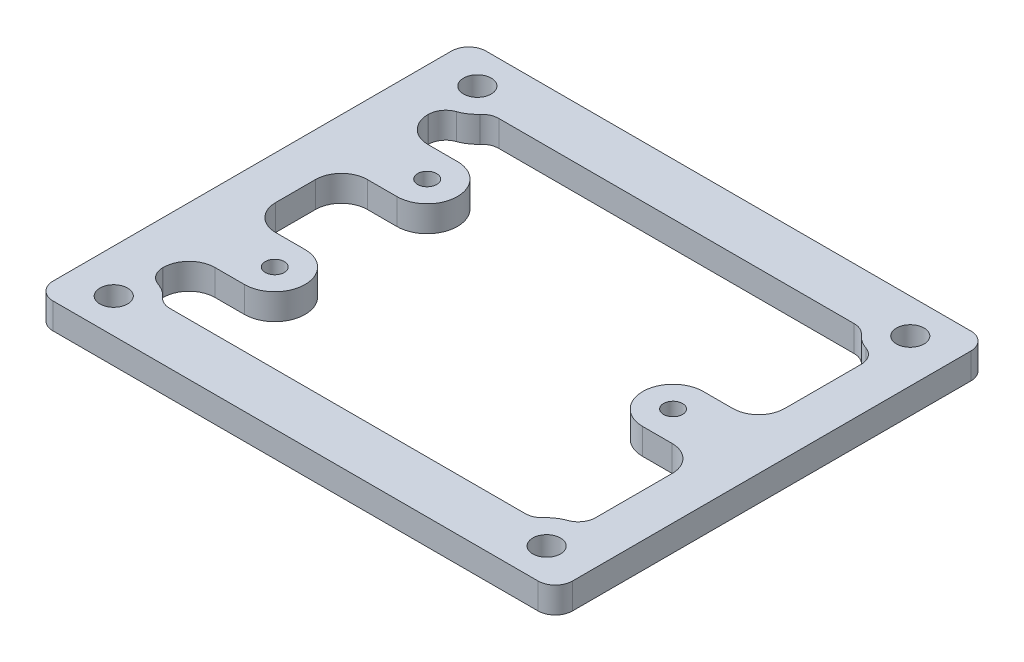
SolidWorks part; units mm, degrees
ref_plane "前视基准面" through (0, 0, 0) normal (0, 0, 1) x (1, 0, 0)
ref_plane "上视基准面" through (0, 0, 0) normal (0, 1, 0) x (1, 0, 0)
ref_plane "右视基准面" through (0, 0, 0) normal (1, 0, 0) x (0, 0, -1)
sketch "草图1" plane through (0, 0, 0) normal (0, 1, 0) x (1, 0, 0)
  line L0 (0, 0) -> (0, 11.3966) construction
  line L1 (-30, 25) -> (30, 25)
  line L2 (-30, 25) -> (-30, -25)
  line L3 (-30, -25) -> (30, -25)
  line L4 (30, 25) -> (30, -25)
  line L5 (-30, 25) -> (30, -25) construction
  line L6 (-30, -25) -> (30, 25) construction
  line L7 (0, 0) -> (7.4363, 0) construction
  line L8 (-25, -5.3) -> (-25, 5.3)
  line L9 (-25, 5.3) -> (-18.6, 5.3)
  line L10 (-25, 17) -> (-25, 12.3)
  line L11 (-25, 12.3) -> (-18.6, 12.3)
  line L12 (-21.5359, 19) -> (21.5359, 19)
  line L13 (25, 17) -> (25, 3.5)
  line L14 (25, 3.5) -> (18.6, 3.5)
  line L15 (25, -3.5) -> (18.6, -3.5)
  line L16 (25, -17) -> (25, -3.5)
  line L17 (-21.5359, -19) -> (21.5359, -19)
  line L18 (-25, -17) -> (-25, -12.3)
  line L19 (-25, -12.3) -> (-18.6, -12.3)
  line L20 (-25, -5.3) -> (-18.6, -5.3)
  circle A0 centre (-25, 21) radius 1.6
  circle A1 centre (25, 21) radius 1.6
  circle A2 centre (25, -21) radius 1.6
  circle A3 centre (-25, -21) radius 1.6
  circle A4 centre (18.6, 0) radius 1.1
  circle A5 centre (-18.6, 8.8) radius 1.1
  circle A6 centre (-18.6, -8.8) radius 1.1
  arc A7 (-18.6, 5.3) -> (-18.6, 12.3) centre (-18.6, 8.8) ccw
  arc A8 (18.6, 3.5) -> (18.6, -3.5) centre (18.6, 0) ccw
  arc A9 (-25, 17) -> (-21.5359, 19) centre (-25, 21) ccw
  arc A10 (25, 17) -> (21.5359, 19) centre (25, 21) cw
  arc A11 (25, -17) -> (21.5359, -19) centre (25, -21) ccw
  arc A12 (-25, -17) -> (-21.5359, -19) centre (-25, -21) cw
  arc A13 (-18.6, -5.3) -> (-18.6, -12.3) centre (-18.6, -8.8) cw
  point P0 (0, 0)
  point P45 (-25, 0)
  dimension "D3" = 3.2
  dimension "D4" = 50
  dimension "D5" = 42
  dimension "D6" = 18.6
  dimension "D7" = 18.6
  dimension "D8" = 8.8
  dimension "D9" = 2.2
  dimension "D11" = 3.5
  dimension "D12" = 4
  dimension "D1" = 60
  dimension "D2" = 50
  dimension "D10" = 5
  dimension "D13" = 5
  dimension "D15" = 6
extrude "凸台-拉伸1" add sketch "草图1" along normal blind 3
fillet "圆角1" radius 2 4 edges at (-30, 1.5, -25) (30, 1.5, -25) (30, 1.5, 25) (-30, 1.5, 25)
fillet "圆角2" radius 2 8 edges at (25, 1.5, -17) (21.5359, 1.5, -19) (21.5359, 1.5, 19) (25, 1.5, 17) (-21.5359, 1.5, 19) (-25, 1.5, 17) (-25, 1.5, -17) (-21.5359, 1.5, -19)
fillet "圆角3" radius 3 6 edges at (25, 1.5, -3.5) (25, 1.5, 3.5) (-25, 1.5, 12.3) (-25, 1.5, 5.3) (-25, 1.5, -5.3) (-25, 1.5, -12.3)
